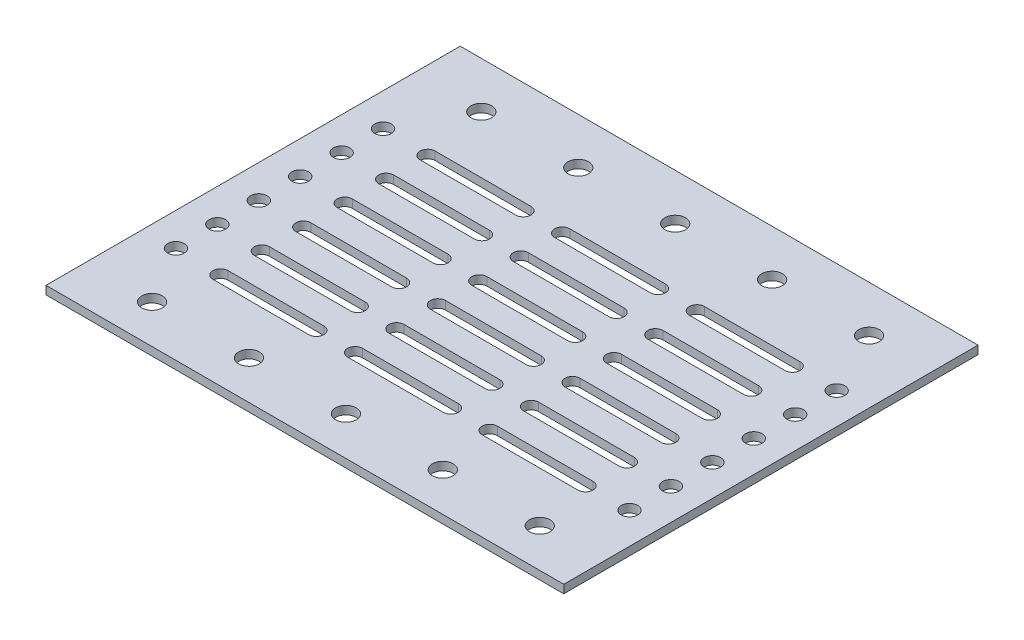
SolidWorks part; units mm, degrees
ref_plane "Front Plane" through (0, 0, 0) normal (0, 0, 1) x (1, 0, 0)
ref_plane "Top Plane" through (0, 0, 0) normal (0, 1, 0) x (1, 0, 0)
ref_plane "Right Plane" through (0, 0, 0) normal (1, 0, 0) x (0, 0, -1)
sketch "Sketch1" plane through (0, 0, 0) normal (0, 1, 0) x (1, 0, 0)
  line L1 (-62.5, 50) -> (62.5, 50)
  line L2 (-62.5, 50) -> (-62.5, -50)
  line L3 (-62.5, -50) -> (62.5, -50)
  line L4 (62.5, 50) -> (62.5, -50)
  line L5 (-62.5, 50) -> (62.5, -50) construction
  line L6 (-62.5, -50) -> (62.5, 50) construction
  point P0 (0, 0)
  dimension "D1" = 125
  dimension "D2" = 100
extrude "Boss-Extrude1" add sketch "Sketch1" along normal blind 2
sketch "Sketch2" plane through (0, 2, 0) normal (0, 1, 0) x (1, 0, 0)
  line L0 (-43.6043, 23.2218) -> (-20.4839, 23.2218) construction
  line L1 (-43.6043, 25.0471) -> (-20.4839, 25.0471)
  line L2 (-43.6043, 21.3965) -> (-20.4839, 21.3965)
  arc A0 (-43.6043, 25.0471) -> (-43.6043, 21.3965) centre (-43.6043, 23.2218) ccw
  arc A1 (-20.4839, 21.3965) -> (-20.4839, 25.0471) centre (-20.4839, 23.2218) ccw
  point P2 (-32.0441, 23.2218)
extrude "Cut-Extrude1" cut sketch "Sketch2" against normal through all contours L1 A1 L2 A0
pattern_linear "LPattern1" count 6 spacing 10 along (0, 0, 1) count 3 spacing 32.5 along (1, 0, 0) of "Cut-Extrude1"
sketch "Sketch3" plane through (0, 2, 0) normal (0, 1, 0) x (1, 0, 0)
  circle A0 centre (-54.556, 23.4246) radius 2
extrude "Cut-Extrude2" cut sketch "Sketch3" against normal through all
pattern_linear "LPattern2" count 6 spacing 10 along (0, 0, 1) count 2 spacing 109.5 along (1, 0, 0) of "Cut-Extrude2"
sketch "Sketch4" plane through (0, 2, 0) normal (0, 1, 0) x (1, 0, 0)
  circle A0 centre (-46.2408, 38.8382) radius 2.5
extrude "Cut-Extrude3" cut sketch "Sketch4" against normal blind 20
pattern_linear "LPattern3" count 5 spacing 23.4 along (1, 0, 0) count 3 spacing 79.5 along (0, 0, 1) of "Cut-Extrude3"
